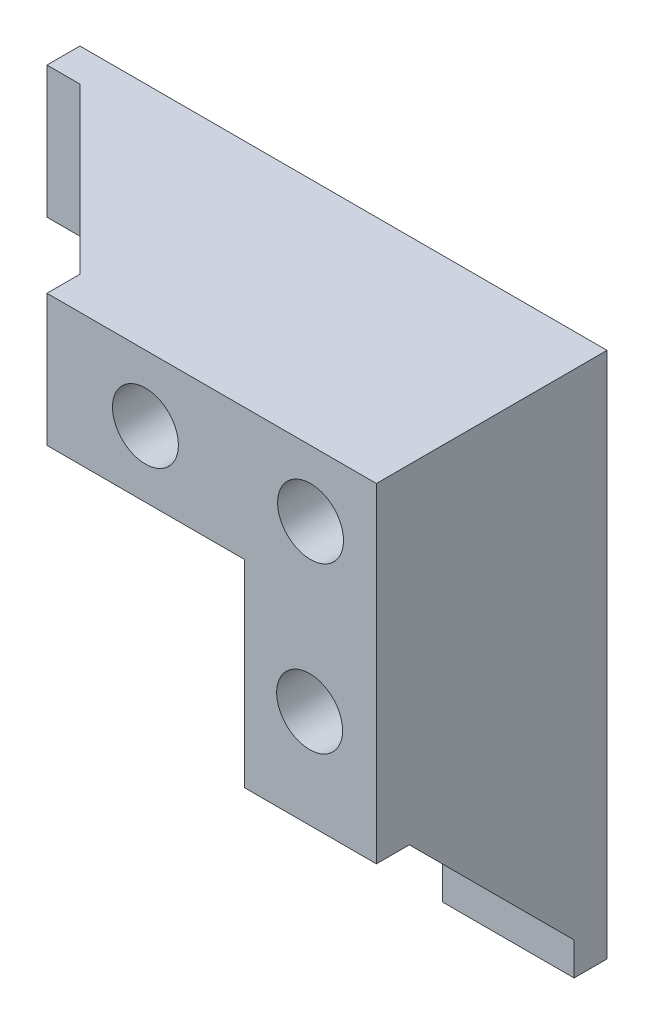
SolidWorks part; units mm, degrees
ref_plane "前视基准面" through (0, 0, 0) normal (0, 0, 1) x (1, 0, 0)
ref_plane "上视基准面" through (0, 0, 0) normal (0, 1, 0) x (1, 0, 0)
ref_plane "右视基准面" through (0, 0, 0) normal (1, 0, 0) x (0, 0, -1)
sketch "草图1" plane through (0, 0, 0) normal (0, 0, 1) x (1, 0, 0)
  line L0 (-30.6207, 42.9655) -> (49.3793, 42.9655)
  line L1 (49.3793, 42.9655) -> (49.3793, -37.0345)
  line L2 (49.3793, -37.0345) -> (29.3793, -37.0345)
  line L3 (29.3793, -37.0345) -> (29.3793, 22.9655)
  line L4 (29.3793, 22.9655) -> (-30.6207, 22.9655)
  line L5 (-30.6207, 22.9655) -> (-30.6207, 42.9655)
  dimension "D1" = 80
  dimension "D2" = 80
  dimension "D3" = 20
  dimension "D4" = 20
extrude "凸台-拉伸1" add sketch "草图1" along normal blind 35
sketch "草图2" plane through (0, 0, 35) normal (0, 0, 1) x (1, 0, 0)
  line L0 (-30.6207, 32.9655) -> (49.3793, 32.9655) construction
  line L1 (-30.6207, 42.9655) -> (-30.6207, 22.9655) construction
  line L2 (49.3793, -37.0345) -> (49.3793, 42.9655) construction
  line L3 (39.3793, -37.0345) -> (39.3793, 42.9655) construction
  line L4 (29.3793, -37.0345) -> (49.3793, -37.0345) construction
  line L5 (49.3793, 42.9655) -> (-30.6207, 42.9655) construction
  line L6 (49.3793, -17.0345) -> (29.3793, -17.0345) construction
  line L7 (29.3793, 22.9655) -> (29.3793, -37.0345) construction
  line L8 (14.3793, 22.9655) -> (14.3793, 42.9655) construction
  line L9 (-30.6207, 22.9655) -> (29.3793, 22.9655) construction
  line L10 (29.3793, 7.9655) -> (49.3793, 7.9655) construction
  line L11 (-10.6207, 22.9655) -> (-10.6207, 42.9655) construction
  dimension "D1" = 20
  dimension "D2" = 25
  dimension "D3" = 20
  dimension "D4" = 25
hole_wizard "孔1" positions "3D草图1" profile "草图3" legacy
sketch3d "3D草图1"
  line L0 (-10.6207, 22.9655, 35) -> (-10.6207, 42.9655, 35) construction
  line L1 (14.3793, 22.9655, 35) -> (14.3793, 42.9655, 35) construction
  line L2 (-30.6207, 32.9655, 35) -> (49.3793, 32.9655, 35) construction
  line L3 (39.3793, -37.0345, 35) -> (39.3793, 42.9655, 35) construction
  line L4 (29.3793, 7.9655, 35) -> (49.3793, 7.9655, 35) construction
  line L5 (49.3793, -17.0345, 35) -> (29.3793, -17.0345, 35) construction
  point P0 (-10.6207, 32.9655, 35)
  point P4 (14.3793, 32.9655, 35)
  point P8 (39.3793, 32.9655, 35)
  point P14 (39.3793, 7.9655, 35)
  point P18 (39.3793, 7.9655, 35)
  point P20 (39.3793, -17.0345, 35)
sketch "草图3" plane through (39.3793, 32.9655, 35) normal (1, 0, 0) x (0, -1, 0)
  line L0 (0, 0) -> (0, 35)
  line L1 (0, 35) -> (2.75, 35)
  line L2 (2.75, 35) -> (2.75, 27)
  line L3 (2.75, 27) -> (5, 27)
  line L4 (5, 27) -> (5, 0)
  line L5 (5, 0) -> (0, 0)
  line L6 (0, 110) -> (0, -10) construction
  dimension "直径" = 5.5
  dimension "深度" = 35
  dimension "柱坑直径" = 10
  dimension "柱坑深度" = 27
sketch "草图6" plane through (0, 0, 35) normal (0, 0, 1) x (1, 0, 0)
  circle A0 centre (14.3244, 32.9855) radius 2.75
  circle A1 centre (-10.6414, 32.9855) radius 2.75
  circle A2 centre (39.2426, 7.9167) radius 2.8612
  circle A3 centre (39.2426, -17.0413) radius 2.75
  circle A4 centre (14.3244, 32.9855) radius 5
  circle A5 centre (39.2426, 7.9167) radius 5
  circle A6 centre (39.2426, -17.0413) radius 5
  circle A7 centre (-10.6414, 32.9855) radius 5
  dimension "D1" = 5.7224
  dimension "D2" = 5.5
  dimension "D3" = 5.5
  dimension "D4" = 5.5
  dimension "D5" = 10
  dimension "D6" = 10
  dimension "D7" = 10
  dimension "D8" = 10
extrude "切除-拉伸1" cut sketch "草图6" against normal blind 27
sketch "草图8" plane through (0, 0, 35) normal (0, 0, 1) x (1, 0, 0)
  circle A1 centre (14.3244, 32.9855) radius 2.75
  circle A2 centre (14.3244, 32.9855) radius 2.75
  circle A3 centre (39.2426, 7.9167) radius 2.8612
  circle A4 centre (39.2426, 7.9167) radius 2.8612
  circle A5 centre (39.2426, -17.0413) radius 2.75
  circle A6 centre (39.2426, -17.0413) radius 2.75
  circle A7 centre (-10.6414, 32.9855) radius 2.75
  circle A8 centre (-10.6414, 32.9855) radius 2.75
  dimension "D1" = 0
  dimension "D2" = 0
  dimension "D3" = 0
  dimension "D4" = 0
extrude "切除-拉伸2" cut sketch "草图8" against normal blind 35
sketch "草图9" plane through (49.3793, 0, 0) normal (1, 0, 0) x (0, 0, -1)
  line L0 (0, -7.0345) -> (-35, -7.0345)
  line L1 (0, -37.0345) -> (0, 42.9655) construction
  line L2 (-35, -37.0345) -> (-35, 42.9655) construction
  line L3 (-35, -37.0345) -> (0, -37.0345) construction
  line L4 (-5, 42.9655) -> (-5, -37.0345)
  line L5 (-35, 42.9655) -> (0, 42.9655) construction
  line L6 (-30, 42.9655) -> (-30, -7.0345)
  line L7 (0, -32.0345) -> (-5, -32.0345)
  line L8 (-5, -32.0345) -> (-30, -7.0345)
  line L9 (-5, -32.0345) -> (-5, -37.0345)
  line L10 (-35, -37.0345) -> (-35, -7.0345)
  line M7 (-35, 42.9655) -> (-35, -37.0345)
  line M8 (-35, -37.0345) -> (0, -37.0345)
  dimension "D1" = 30
  dimension "D2" = 5
  dimension "D3" = 5
  dimension "D4" = 5
extrude "切除-拉伸3" cut sketch "草图9" against normal blind 35 contours L4 L8 L0 M7 M8
sketch "草图10" plane through (0, 42.9655, 0) normal (0, 1, 0) x (1, 0, 0)
  line L0 (-0.6207, -35) -> (-0.6207, 0)
  line L1 (49.3793, -35) -> (-30.6207, -35) construction
  line L2 (49.3793, 0) -> (-30.6207, 0) construction
  line L3 (49.3793, -30) -> (-0.6207, -30)
  line L4 (49.3793, -35) -> (49.3793, 0) construction
  line L5 (-30.6207, -35) -> (-30.6207, 0) construction
  line L6 (-0.6207, -35) -> (-30.6207, -35)
  line L7 (49.3793, -5) -> (-30.6207, -5)
  line L8 (-0.6207, -30) -> (-25.6207, -5)
  line L9 (-30.6207, -35) -> (-30.6207, -5)
  line M6 (-30.6207, 0) -> (-30.6207, -35)
  line M7 (-30.6207, -35) -> (49.3793, -35)
  dimension "D1" = 30
  dimension "D2" = 5
  dimension "D4" = 5
extrude "切除-拉伸4" cut sketch "草图10" against normal blind 35 contours L0 L8 L7 M6 M7
